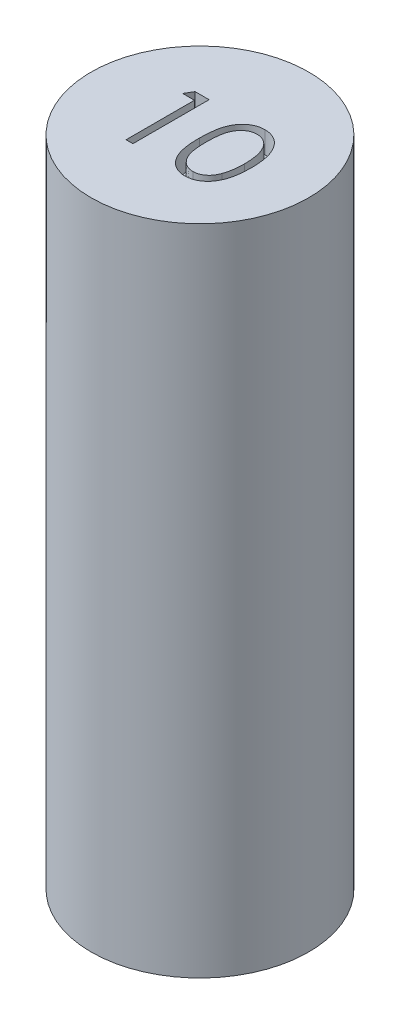
SolidWorks part; units mm, degrees
ref_plane "Front Plane" through (0, 0, 0) normal (0, 0, 1) x (1, 0, 0)
ref_plane "Top Plane" through (0, 0, 0) normal (0, 1, 0) x (1, 0, 0)
ref_plane "Right Plane" through (0, 0, 0) normal (1, 0, 0) x (0, 0, -1)
sketch "Sketch1" plane through (0, 0, 0) normal (0, 1, 0) x (1, 0, 0)
  circle A0 centre (0, 0) radius 5
  dimension "D1" = 10
extrude "Boss-Extrude1" add sketch "Sketch1" along normal blind 30
sketch "Sketch2" plane through (0, 30, 0) normal (0, 1, 0) x (1, 0, 0)
  text T0 "10"
extrude "Cut-Extrude1" cut sketch "Sketch2" against normal blind 1
